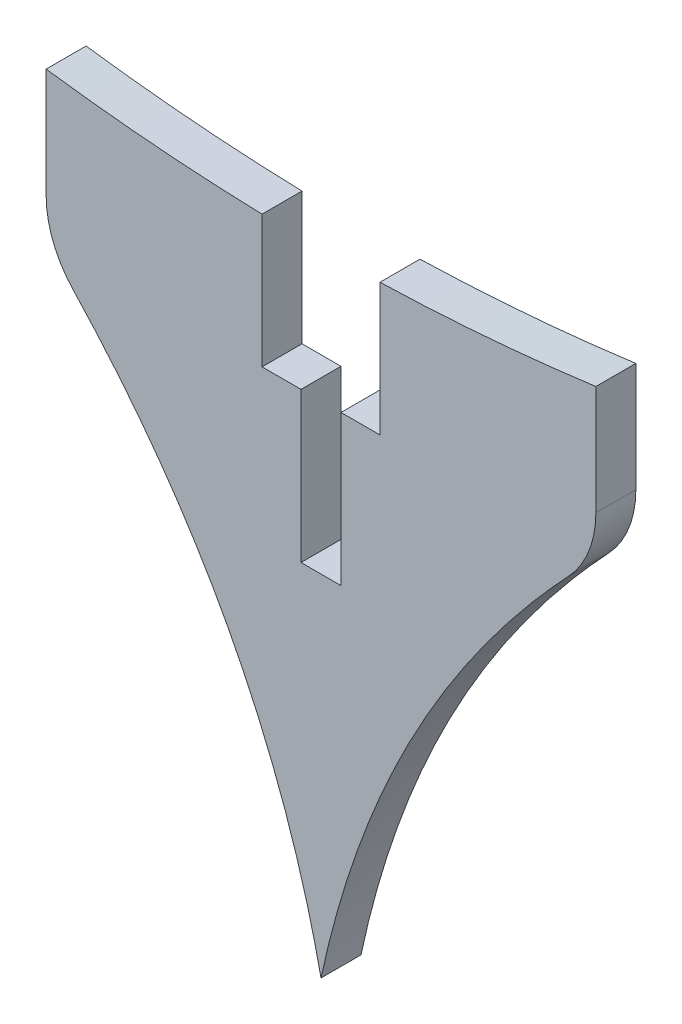
SolidWorks part; units mm, degrees
material "Acier S235"
ref_plane "Plan de face" through (0, 0, 0) normal (0, 0, 1) x (1, 0, 0)
ref_plane "Plan de dessus" through (0, 0, 0) normal (0, 1, 0) x (1, 0, 0)
ref_plane "Plan de droite" through (0, 0, 0) normal (1, 0, 0) x (0, 0, -1)
sketch "Esquisse1" plane through (0, 0, 0) normal (0, 0, 1) x (1, 0, 0)
  line L0 (-27.5, 17.5) -> (27.5, 17.5) construction
  line L2 (-27.5, 32.5) -> (-27.5, 17.5)
  line L5 (-5.9, 30.732) -> (-5.9, 17.5)
  line L7 (0, 30.6471) -> (0, -32.5) construction
  line L12 (-2, 17.5) -> (-2, 2.5)
  line L13 (-2, 2.5) -> (2, 2.5)
  line L14 (-5.9, 17.5) -> (-2, 17.5)
  line L15 (27.5, 32.5) -> (27.5, 17.5)
  line L17 (5.9, 30.732) -> (5.9, 17.5)
  line L18 (5.9, 17.5) -> (2, 17.5)
  line L19 (2, 17.5) -> (2, 2.5)
  line L20 (0, 30.6471) -> (0, 235.6471) construction
  line L21 (0, -35.75) -> (0, 35.75) construction
  arc A0 (-27.5, 32.5) -> (-5.9, 30.732) centre (0, 235.6471) ccw
  arc A1 (5.9, 30.732) -> (27.5, 32.5) centre (0, 235.6471) ccw
  circle A2 centre (0, 235.6471) radius 205 construction
  spline S0 degree 2 poles (-27.5, 17.5) (-6.1294, -3.7008) (0, -32.5) knots 0 0 0 1 1 1
  spline S1 degree 2 poles (27.5, 17.5) (6.1294, -3.7008) (0, -32.5) knots 0 0 0 1 1 1
  point P0 (0, 0)
  point P12 (0, 17.5)
  point P20 (0, 2.5)
  dimension "D2" = 205
  dimension "D1" = 11.8
  dimension "D3" = 55
  dimension "D4" = 205
  dimension "D5" = 2
  dimension "D6" = 15
  dimension "D7" = 65
  dimension "D8" = 20
  dimension "D9" = 13.1471
  dimension "D10" = 13
extrude "Boss.-Extru.1" add sketch "Esquisse1" along normal blind 4
sketch "Esquisse2" plane through (0, 0, 0) normal (1, 0, 0) x (0, 0, -1)
  line L0 (-4, 17.5) -> (0, 17.5) construction
  line L2 (-29.5, 30.65) -> (-29.5, 17.5)
  line L5 (-6, 30.65) -> (-6, 17.5)
  line L6 (-6, 17.5) -> (2, 17.5)
  line L7 (-4, 17.5) -> (-29.5, 17.5) construction
  line L10 (-4, 2.5) -> (0, 2.5)
  line L11 (-2, 32.5) -> (-2, -32.5) construction
  line L12 (-29.5, 30.65) -> (-6, 30.65)
  line L14 (0, 17.5) -> (0, -32.5) construction
  line L15 (-4, -32.5) -> (0, -32.5) construction
  line L16 (0, -25.1232) -> (0, 2.5)
  line L18 (25.5, 30.65) -> (25.5, 17.5)
  line L19 (25.5, 30.65) -> (2, 30.65)
  line L20 (2, 30.65) -> (2, 17.5)
  line L21 (-4, -25.1232) -> (-4, 2.5)
  spline S0 degree 2 poles (-29.5, 17.5) (-12.7387, -1.6729) (-4, -25.1232) knots 0 0 0 1 1 1
  spline S2 degree 2 poles (25.5, 17.5) (8.7387, -1.6729) (0, -25.1232) knots 0 0 0 1 1 1
  point P0 (-2, 17.5)
  point P15 (-2, 2.5)
  point P27 (-2, 17.5)
  dimension "D1" = 55
  dimension "D2" = 13.15
  dimension "D4" = 8
extrude "Boss.-Extru.2" [suppressed] add sketch "Esquisse2" along normal mid plane 4 separate body
fillet "Congé1" radius 10 2 edges at (-27.5, 17.5, 2) (27.5, 17.5, 2)
fillet "Congé2" [suppressed] radius 10
